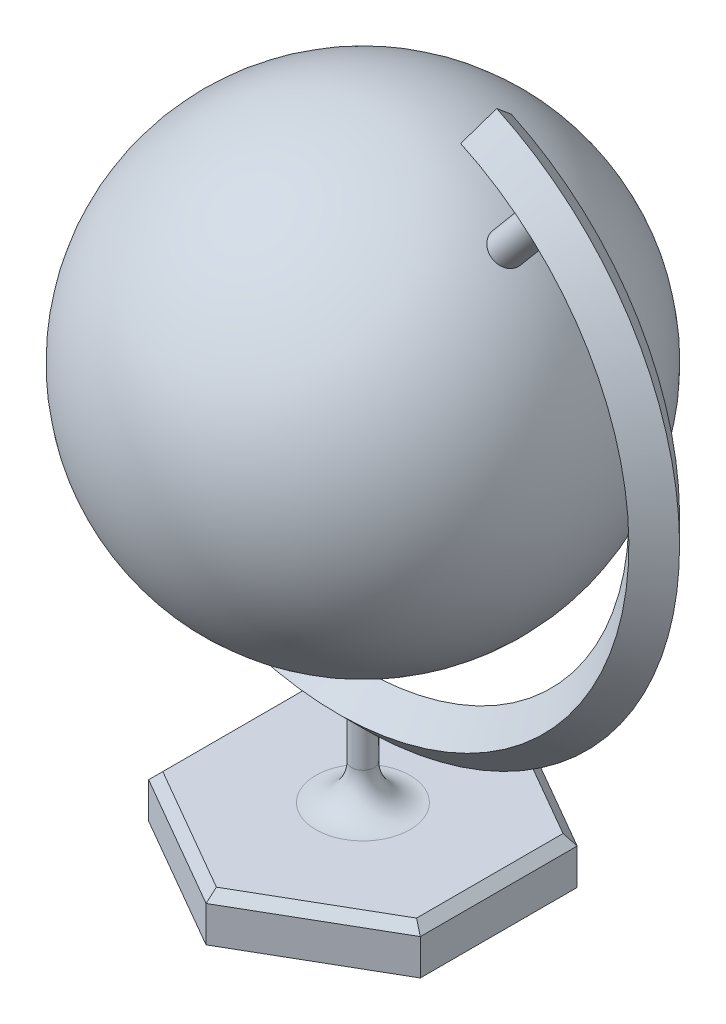
SolidWorks part; units mm, degrees
ref_plane "Front Plane" through (0, 0, 0) normal (0, 0, 1) x (1, 0, 0)
ref_plane "Top Plane" through (0, 0, 0) normal (0, 1, 0) x (1, 0, 0)
ref_plane "Right Plane" through (0, 0, 0) normal (1, 0, 0) x (0, 0, -1)
sketch "Sketch1" plane through (0, 0, 0) normal (0, 1, 0) x (1, 0, 0)
  line L1 (0, 35) -> (-30.3109, 17.5)
  line L2 (-30.3109, 17.5) -> (-30.3109, -17.5)
  line L3 (-30.3109, -17.5) -> (0, -35)
  line L4 (0, -35) -> (30.3109, -17.5)
  line L5 (30.3109, -17.5) -> (30.3109, 17.5)
  line L6 (30.3109, 17.5) -> (0, 35)
  circle A0 centre (0, 0) radius 30.3109 construction
  dimension "D1" = 70
extrude "Boss-Extrude1" add sketch "Sketch1" along normal blind 10
shell "Shell1" thickness 2
sketch "Sketch2" plane through (0, 0, 0) normal (0, 0, 1) x (1, 0, 0)
  line L0 (0, 145) -> (0, 45)
  arc A0 (0, 45) -> (0, 145) centre (0, 95) ccw
  dimension "D1" = 50
  dimension "D2" = 95
other "AlignGroup1"
revolve "Revolve1" add sketch "Sketch2" angle 360 about L0
ref_point "Point1"
sketch "Sketch4" plane through (0, 0, 0) normal (1, 0, 0) x (0, 0, -1)
  line L0 (0, 24.3431) -> (-5.6569, 30)
  line L1 (-5.6569, 30) -> (0, 35.6569)
  line L2 (0, 35.6569) -> (5.6569, 30)
  line L3 (5.6569, 30) -> (0, 24.3431)
  line L4 (0, 95) -> (-58.7543, 95) construction
  dimension "D1" = 8
  dimension "D2" = 65
revolve "Revolve-Thin1" add sketch "Sketch4" angle 55 about L4
ref_plane "Plane1" through (46.7784, 55.7483, 0) normal (0.6428, 0.766, 0) x (0, 0, 1)
sketch "Sketch5" plane through (46.7784, 55.7483, 0) normal (0.6428, 0.766, 0) x (0, 0, 1)
  circle A0 centre (0, -61.0648) radius 3.5
  dimension "D1" = 7
extrude "Boss-Extrude2" add sketch "Sketch5" along normal up to body and the other way up to body
sketch "Sketch6" plane through (0, 10, 0) normal (0, 1, 0) x (1, 0, 0)
  circle A0 centre (0, 0) radius 2.5
  dimension "D1" = 5
extrude "Boss-Extrude3" add sketch "Sketch6" along normal up to next
fillet "Fillet1" radius 8 1 edges at (0, 10, 2.5)
chamfer "Chamfer1" distance 2 angle 45 6 edges at (-15.1554, 10, 26.25) (-30.3109, 10, 0) (-15.1554, 10, -26.25) (15.1554, 10, -26.25) (30.3109, 10, 0) (15.1554, 10, 26.25)
